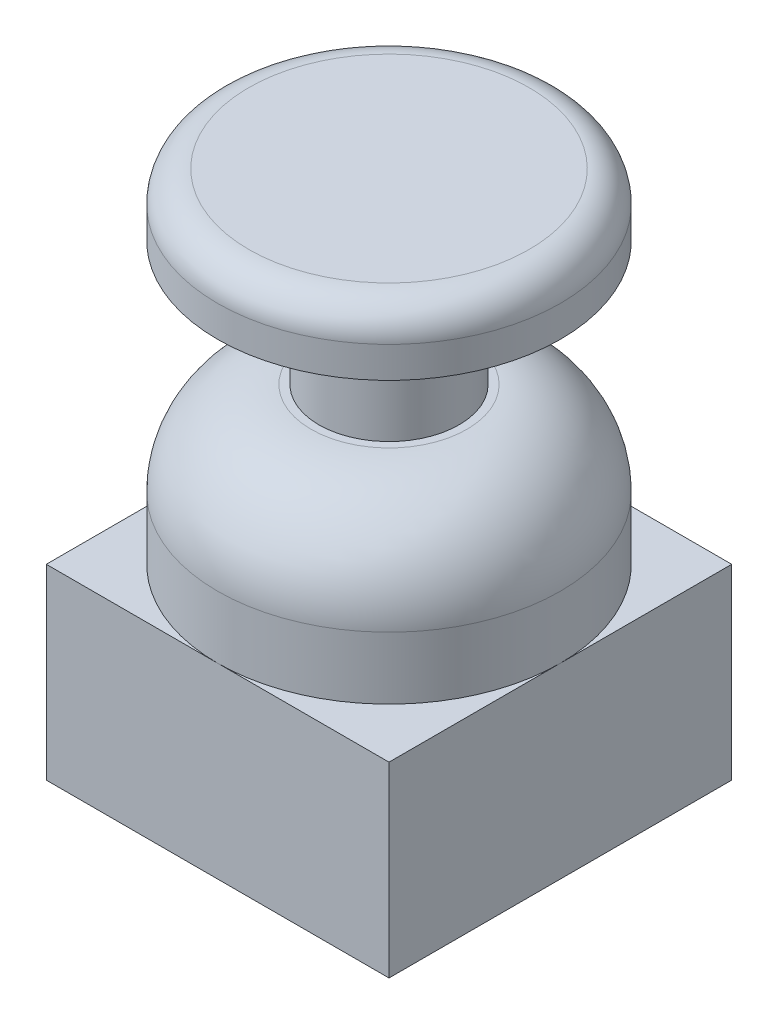
SolidWorks part; units mm, degrees
ref_plane "Front Plane" through (0, 0, 0) normal (0, 0, 1) x (1, 0, 0)
ref_plane "Top Plane" through (0, 0, 0) normal (0, 1, 0) x (1, 0, 0)
ref_plane "Right Plane" through (0, 0, 0) normal (1, 0, 0) x (0, 0, -1)
sketch "Sketch1" plane through (0, 0, 0) normal (0, 0, 1) x (1, 0, 0)
  line L0 (0, 0) -> (-11, 0)
  line L1 (-11, 0) -> (-11, 16)
  line L2 (-5, 22) -> (-4.5, 22)
  line L3 (-4.5, 22) -> (-4.5, 30)
  line L4 (-4.5, 30) -> (-11, 30)
  line L5 (-11, 30) -> (-11, 32)
  line L6 (-9, 34) -> (0, 34)
  line L7 (0, 34) -> (0, 0)
  arc A0 (-11, 32) -> (-9, 34) centre (-9, 32) cw
  arc A1 (-11, 16) -> (-5, 22) centre (-5, 16) cw
  point P11 (-11, 34)
  point P14 (-11, 22)
  dimension "D6" = 2
  dimension "D7" = 6
  dimension "D1" = 22
  dimension "D2" = 8
  dimension "D3" = 4
  dimension "D4" = 11
  dimension "D5" = 4.5
revolve "Stick Revolve" add sketch "Sketch1" angle 360 about L7
sketch "Sketch2" plane through (0, 0, 0) normal (0, -1, 0) x (1, 0, 0)
  line L1 (11, -11) -> (-11, -11)
  line L2 (11, -11) -> (11, 11)
  line L3 (11, 11) -> (-11, 11)
  line L4 (-11, -11) -> (-11, 11)
  line L5 (11, -11) -> (-11, 11) construction
  line L6 (11, 11) -> (-11, -11) construction
  circle A0 centre (0, 0) radius 11 construction
  point P0 (0, 0)
extrude "Switch Base" add sketch "Sketch2" against normal blind 12
